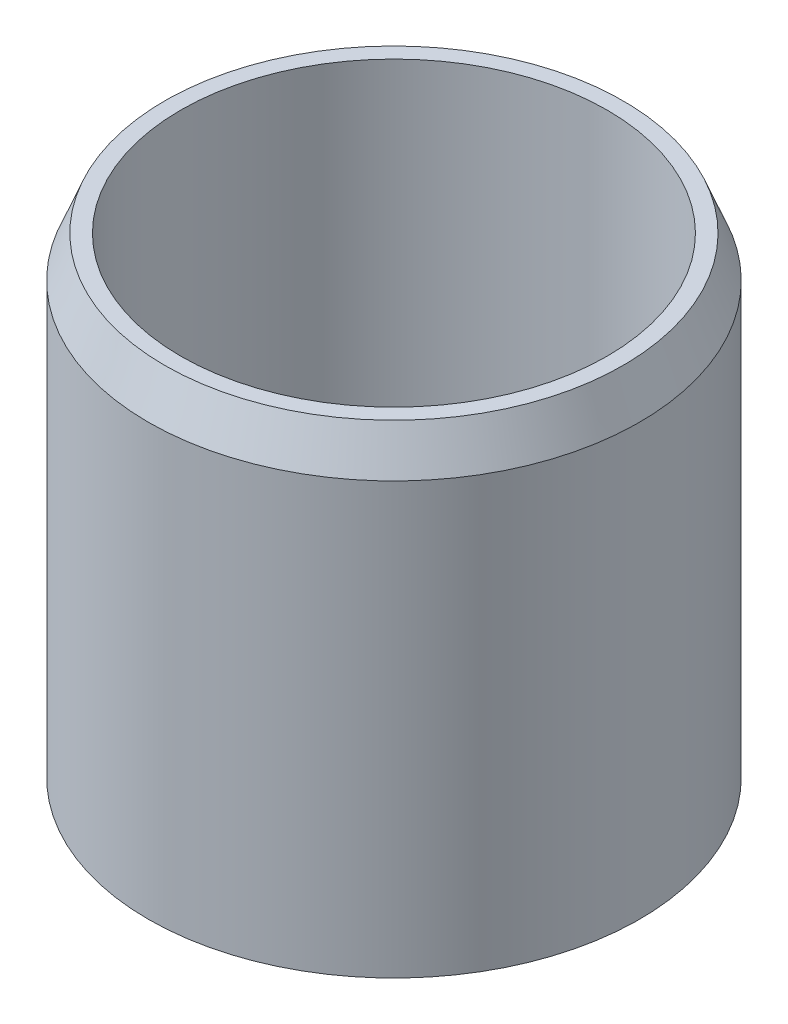
SolidWorks part; units mm, degrees
material "ABS"
ref_plane "Front Plane" through (0, 0, 0) normal (0, 0, 1) x (1, 0, 0)
ref_plane "Top Plane" through (0, 0, 0) normal (0, 1, 0) x (1, 0, 0)
ref_plane "Right Plane" through (0, 0, 0) normal (1, 0, 0) x (0, 0, -1)
sketch "Sketch1" plane through (0, 0, 0) normal (0, 1, 0) x (1, 0, 0)
  line L6 (0, 12.7) -> (0, 33.02)
  circle A0 centre (0, 0) radius 38.0365
  circle A1 centre (0, 0) radius 6.5024
  circle A2 centre (0, 0) radius 12.7
  circle A3 centre (0, 0) radius 33.02
  circle A4 centre (0, 22.86) radius 7.62
  circle A5 centre (21.7412, 7.0641) radius 7.62
  circle A6 centre (13.4368, -18.4941) radius 7.62
  circle A7 centre (-13.4368, -18.4941) radius 7.62
  circle A8 centre (-21.7412, 7.0641) radius 7.62
  point P26 (0, 0)
  dimension "D1" = 76.073
  dimension "D2" = 13.0048
  dimension "D6" = 25.4
  dimension "D7" = 66.04
  dimension "D8" = 15.24
  dimension "D9" = 5
extrude "Boss-Extrude1" add sketch "Sketch1" along normal blind 9.525
sketch "Sketch2" plane through (0, 9.525, 0) normal (0, 1, 0) x (1, 0, 0)
  circle A0 centre (0, 0) radius 38.0365
  circle A1 centre (0, 0) radius 33.02
  dimension "D1" = 76.073
  dimension "D2" = 66.04
extrude "Boss-Extrude2" add sketch "Sketch2" along normal blind 63.5
sketch "Sketch3" plane through (0, 9.525, 0) normal (0, 1, 0) x (1, 0, 0)
  circle A0 centre (0, 0) radius 12.7
  circle A2 centre (0, 0) radius 6.5024
  dimension "D1" = 25.4
  dimension "D2" = 13.0048
extrude "Boss-Extrude3" add sketch "Sketch3" along normal blind 15.875
chamfer "Chamfer1" distance 6.35 distance2 2.54 1 edges at (0, 73.025, 38.0365)
sketch "Sketch4" plane through (0, 25.4, 0) normal (0, 1, 0) x (1, 0, 0)
  circle A0 centre (0, 0) radius 12.7
  dimension "D1" = 25.4
extrude "Boss-Extrude4" add sketch "Sketch4" along normal blind 6.35
fillet "Fillet1" radius 2.54 1 edges at (0, 31.75, 12.7)
